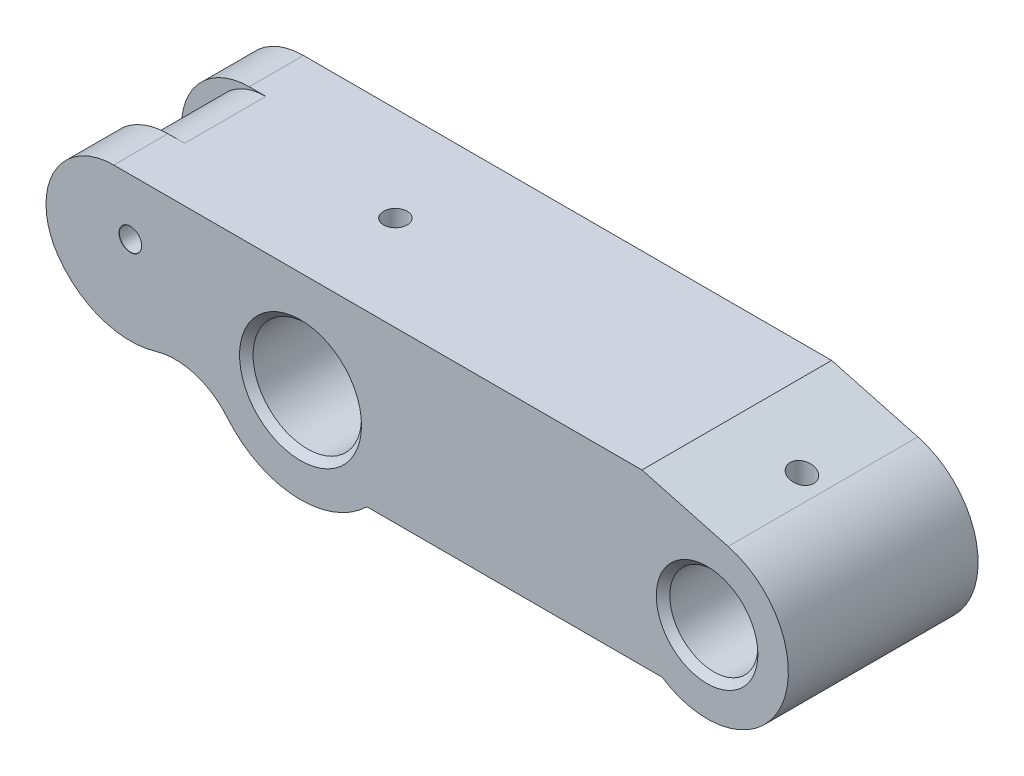
SolidWorks part; units mm, degrees
ref_plane "前视基准面" through (0, 0, 0) normal (0, 0, 1) x (1, 0, 0)
ref_plane "上视基准面" through (0, 0, 0) normal (0, 1, 0) x (1, 0, 0)
ref_plane "右视基准面" through (0, 0, 0) normal (1, 0, 0) x (0, 0, -1)
other "Configuration Table"
sketch "草图1" plane through (0, 0, 0) normal (0, 0, 1) x (1, 0, 0)
  line L0 (0, 0) -> (71.3653, 0) construction
  line L1 (9.798, -10) -> (53.3668, -10)
  line L2 (-27.5655, 15) -> (50.3837, 15)
  line L3 (50.3837, 15) -> (63.1058, 11.5911)
  line L4 (0, 0) -> (-46.5774, 0) construction
  line L5 (-25.1141, 6.7293) -> (0, 0) construction
  arc A0 (-10.7877, -8.9233) -> (9.798, -10) centre (0, 0) ccw
  arc A1 (53.3668, -10) -> (63.1058, 11.5911) centre (60, 0) ccw
  arc A2 (-27.5655, 15) -> (-35.737, -0.7643) centre (-27.5655, 5) ccw
  arc A3 (-35.737, -0.7643) -> (-21.3718, -5.7204) centre (-25.1141, 6.7293) ccw
  arc A4 (-21.3718, -5.7204) -> (-10.7877, -8.9233) centre (-18.4932, -15.2971) cw
  dimension "D1" = 28
  dimension "D2" = 24
  dimension "D7" = 10
  dimension "D8" = 13
  dimension "D9" = 10
  dimension "D3" = 60
  dimension "D4" = 10
  dimension "D5" = 15
  dimension "D6" = 25
  dimension "D10" = 26
  dimension "D11" = 15
extrude "凸台-拉伸1" add sketch "草图1" along normal mid plane 28
sketch "草图2" plane through (0, 0, 0) normal (0, 0, 1) x (1, 0, 0)
  line L0 (-27.5655, 15) -> (50.3837, 15) construction
  line L1 (-25.1141, 15) -> (-25.8802, 19.2944)
  line L2 (-25.8802, 19.2944) -> (-38.3017, 16.648)
  line L3 (-38.3017, 16.648) -> (-39.0578, 0.338)
  line L4 (-39.0578, 0.338) -> (-36.8736, -9.9147)
  line L5 (-36.8736, -9.9147) -> (-21.9917, -16.8362)
  line L6 (-21.9917, -16.8362) -> (-15.8349, -12.4616)
  line L7 (-15.8349, -12.4616) -> (-10.7877, -8.9233)
  arc A0 (-25.1141, 15) -> (-23.0599, -1.2823) centre (-25.1141, 6.7293) ccw
  arc A1 (-23.0599, -1.2823) -> (-10.7877, -8.9233) centre (-20.5762, -10.9689) cw
  arc A2 (-10.7877, -8.9233) -> (-21.3718, -5.7204) centre (-18.4932, -15.2971) ccw construction
  arc A4 (-10.7877, -8.9233) -> (9.798, -10) centre (0, 0) ccw construction
  point P1 (0, 0)
  dimension "D1" = 10
extrude "切除-拉伸1" cut sketch "草图2" against normal mid plane 12
sketch "草图3" plane through (0, 0, 14) normal (0, 0, 1) x (1, 0, 0)
  circle A0 centre (0, 0) radius 8
  dimension "D1" = 16
extrude "切除-拉伸2" cut sketch "草图3" against normal through all and the other way through all
sketch "草图4" plane through (0, 0, 14) normal (0, 0, 1) x (1, 0, 0)
  circle A0 centre (60, 0) radius 6.5
  dimension "D1" = 13
extrude "切除-拉伸3" cut sketch "草图4" against normal through all
sketch "草图5" plane through (0, 0, 0) normal (0, 1, 0) x (1, 0, 0)
  circle A0 centre (0, 0) radius 1.75
  dimension "D1" = 3.5
extrude "切除-拉伸4" cut sketch "草图5" along normal through all
sketch "草图6" plane through (0, 0, 0) normal (0, 1, 0) x (1, 0, 0)
  circle A0 centre (60, 0) radius 1.75
  dimension "D1" = 3.5
  dimension "D2" = 60
extrude "切除-拉伸5" cut sketch "草图6" along normal through all
sketch "草图7" plane through (0, 0, 14) normal (0, 0, 1) x (1, 0, 0)
  circle A0 centre (-25.1141, 6.7293) radius 2.5604
hole_wizard "M4 螺纹孔的螺纹孔钻头1" positions "3D草图3" profile "草图10" hole size "M4" standard "GB"
sketch3d "3D草图3"
  point P0 (-25.1141, 6.7293, 14)
  point P3 (-25.1141, 6.7293, 14)
sketch "草图10" plane through (-25.1141, 6.7293, 14) normal (1, 0, 0) x (0, -1, 0)
  line L0 (0, 0) -> (0, 8.9914)
  line L1 (0, 8.9914) -> (1.65, 8)
  line L2 (1.65, 8) -> (1.65, 0.025)
  line L3 (1.65, 0.025) -> (1.675, 0)
  line L5 (1.675, 0) -> (0, 0)
  line L6 (-1.65, 0.025) -> (-1.675, 0) construction
  line L10 (0, 8.9914) -> (-1.65, 8) construction
  line L11 (0, -6.35) -> (0, 107.95) construction
  dimension "孔直径" = 3.3
  dimension "孔深度" = 8
  dimension "近端锥形沉头孔直径" = 3.35
  dimension "近端锥形沉头孔角度" = 90
  dimension "导头角度" = 118
mirror "镜向1" about plane through (0, 0, 0) normal (0, 0, 1) of "M4 螺纹孔的螺纹孔钻头1"
sketch "草图11" plane through (0, 0, 14) normal (0, 0, 1) x (1, 0, 0)
  circle A0 centre (-25.1141, 6.7293) radius 1.5
  dimension "D1" = 3
extrude "切除-拉伸6" cut sketch "草图11" against normal through all
chamfer "倒角1" distance 1 angle 45 4 edges at (66.5, 0, 14) (66.5, 0, -14) (8, 0, -14) (8, 0, 14)
